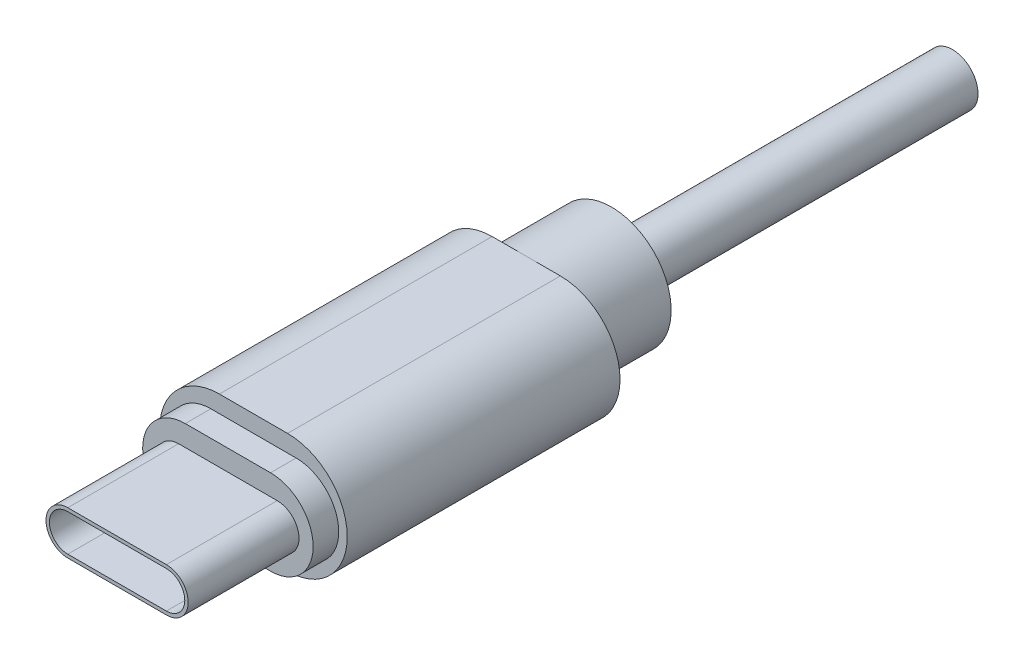
SolidWorks part; units mm, degrees
ref_plane "Front Plane" through (0, 0, 0) normal (0, 0, 1) x (1, 0, 0)
ref_plane "Top Plane" through (0, 0, 0) normal (0, 1, 0) x (1, 0, 0)
ref_plane "Right Plane" through (0, 0, 0) normal (1, 0, 0) x (0, 0, -1)
ref_plane "Plane1" through (0, 0, -1.5) normal (0, 0, 1) x (1, 0, 0)
sketch "Sketch1" plane through (0, 0, -1.5) normal (0, 0, 1) x (1, 0, 0)
  line L0 (2, 3.5) -> (-2, 3.5)
  line L1 (-2, -3.5) -> (2, -3.5)
  arc A0 (-2, 3.5) -> (-2, -3.5) centre (-2, 0) ccw
  arc A1 (2, -3.5) -> (2, 3.5) centre (2, 0) ccw
extrude "Boss-Extrude1" add sketch "Sketch1" against normal blind 16
sketch "Sketch2" plane through (0, 0, -1.5) normal (0, 0, 1) x (1, 0, 0)
  line L0 (2.5, -2.5) -> (-2.5, -2.5)
  line L1 (-2.5, 2.5) -> (2.5, 2.5)
  arc A0 (2.5, 2.5) -> (2.5, -2.5) centre (2.5, 0) cw
  arc A1 (-2.5, -2.5) -> (-2.5, 2.5) centre (-2.5, 0) cw
extrude "Boss-Extrude2" add sketch "Sketch2" along normal blind 1.5
sketch "Sketch3" plane through (0, 0, 0) normal (0, 0, 1) x (1, 0, 0)
  line L0 (2.89, -1.28) -> (-2.89, -1.28)
  line L1 (-2.89, 1.28) -> (2.89, 1.28)
  arc A0 (2.89, 1.28) -> (2.89, -1.28) centre (2.89, 0) cw
  arc A1 (-2.89, -1.28) -> (-2.89, 1.28) centre (-2.89, 0) cw
extrude "Boss-Extrude3" add sketch "Sketch3" along normal blind 6.5
sketch "Sketch4" plane through (0, 0, 6.5) normal (0, 0, 1) x (1, 0, 0)
  line L0 (2.89, 1.08) -> (-2.89, 1.08)
  line L1 (-2.89, -1.08) -> (2.89, -1.08)
  arc A0 (2.89, -1.08) -> (2.89, 1.08) centre (2.89, 0) ccw
  arc A1 (-2.89, 1.08) -> (-2.89, -1.08) centre (-2.89, 0) ccw
extrude "Cut-Extrude1" cut sketch "Sketch4" against normal blind 6.3
ref_plane "Plane2" through (0, 0, 0) normal (0, -1, 0) x (1, 0, 0)
sketch "Sketch5" plane through (0, 0, 0) normal (0, -1, 0) x (1, 0, 0)
  line L0 (3.5, -17.5) -> (0, -17.5)
  line L1 (0, -17.5) -> (0, -122.5)
  line L2 (0, -122.5) -> (1.5, -122.5)
  line L3 (1.5, -122.5) -> (1.5, -22.5)
  line L4 (1.5, -22.5) -> (3.5, -22.5)
  line L5 (3.5, -22.5) -> (3.5, -17.5)
  line L6 (0, -17.5) -> (0, -122.5) construction
revolve "Revolve1" add sketch "Sketch5" angle 360 about L6
sketch "Sketch6" plane through (0, 0, -122.5) normal (0, 0, -1) x (-1, 0, 0)
  circle A1 centre (0, 0) radius 1.5
  circle A2 centre (0, 0) radius 1.5
  dimension "D1" = 0
extrude "Cut-Extrude2" cut sketch "Sketch6" against normal blind 80
